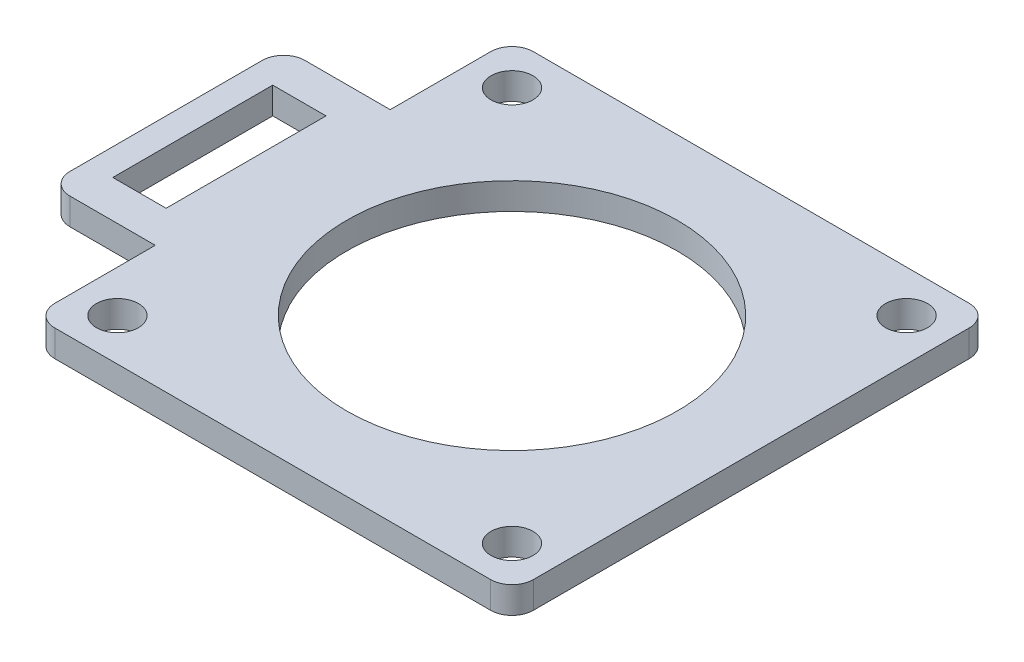
SolidWorks part; units mm, degrees
ref_plane "Front Plane" through (0, 0, 0) normal (0, 0, 1) x (1, 0, 0)
ref_plane "Top Plane" through (0, 0, 0) normal (0, 1, 0) x (1, 0, 0)
ref_plane "Right Plane" through (0, 0, 0) normal (1, 0, 0) x (0, 0, -1)
sketch "Sketch1" plane through (0, 0, 0) normal (0, 1, 0) x (1, 0, 0)
  line L0 (-13.9933, 28.5) -> (-25.96, 28.5)
  line L1 (25.96, -28.5) -> (13.9933, -28.5)
  line L2 (28.5, -25.96) -> (28.5, -13.9933)
  line L3 (25.96, 28.5) -> (13.9933, 28.5)
  line L4 (-28.5, -25.96) -> (-28.5, -13.9933)
  line L5 (28.5, -28.5) -> (-28.5, 28.5) construction
  line L6 (28.5, 28.5) -> (-28.5, -28.5) construction
  line L7 (28.5, 13.9933) -> (28.5, 25.96)
  line L8 (-13.9933, -28.5) -> (-25.96, -28.5)
  line L9 (-28.5, 13.9933) -> (-28.5, 25.96)
  line L11 (-13.9933, -28.5) -> (13.9933, -28.5)
  line L12 (-13.9933, 28.5) -> (13.9933, 28.5)
  line L13 (28.5, 13.9933) -> (28.5, -13.9933)
  line L14 (-28.5, 13.9933) -> (28.5, 13.9933) construction
  line L15 (-28.5, 13.9933) -> (-38.66, 13.9933)
  line L17 (-28.5, -13.9933) -> (-38.66, -13.9933)
  line L18 (-41.2, 11.4533) -> (-41.2, -11.4533)
  line L19 (-28.5, -13.9933) -> (28.5, -13.9933) construction
  line L20 (-34.85, -9.525) -> (-34.85, -13.9933) construction
  line L21 (-38.025, 9.525) -> (-31.675, 9.525)
  line L22 (-38.025, 9.525) -> (-38.025, -9.525)
  line L23 (-38.025, -9.525) -> (-31.675, -9.525)
  line L24 (-31.675, 9.525) -> (-31.675, -9.525)
  line L25 (-34.85, 9.525) -> (-34.85, 13.9933) construction
  circle A0 centre (0, 0) radius 19.685
  arc A5 (-25.96, -28.5) -> (-28.5, -25.96) centre (-25.96, -25.96) cw
  arc A6 (25.96, -28.5) -> (28.5, -25.96) centre (25.96, -25.96) ccw
  arc A7 (28.5, 25.96) -> (25.96, 28.5) centre (25.96, 25.96) ccw
  arc A8 (-25.96, 28.5) -> (-28.5, 25.96) centre (-25.96, 25.96) ccw
  circle A9 centre (-23.5, 23.5) radius 2.5
  circle A10 centre (23.5, 23.5) radius 2.5
  circle A11 centre (23.5, -23.5) radius 2.5
  circle A12 centre (-23.5, -23.5) radius 2.5
  arc A13 (-38.66, -13.9933) -> (-41.2, -11.4533) centre (-38.66, -11.4533) cw
  arc A14 (-38.66, 13.9933) -> (-41.2, 11.4533) centre (-38.66, 11.4533) ccw
  point P38 (0, 0)
  point P50 (-41.2, 13.9933)
  dimension "D1" = 27.9866
  dimension "D4" = 2.54
  dimension "D5" = 39.37
  dimension "D6" = 5
  dimension "D13" = 2.54
  dimension "D2" = 57
  dimension "D3" = 57
  dimension "D7" = 5
  dimension "D9" = 12.7
  dimension "D10" = 19.05
  dimension "D11" = 6.35
  dimension "D12" = 3.175
  dimension "D8" = 4
extrude "Boss-Extrude1" add sketch "Sketch1" along normal blind 3.175
